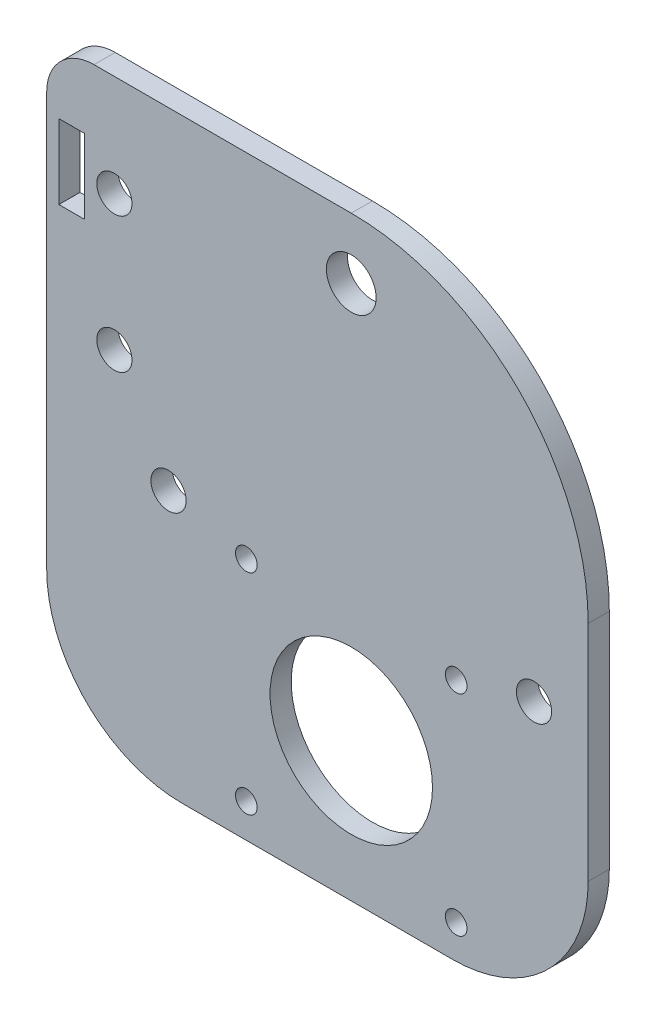
SolidWorks part; units mm, degrees
ref_plane "Front Plane" through (0, 0, 0) normal (0, 0, 1) x (1, 0, 0)
ref_plane "Top Plane" through (0, 0, 0) normal (0, 1, 0) x (1, 0, 0)
ref_plane "Right Plane" through (0, 0, 0) normal (1, 0, 0) x (0, 0, -1)
sketch "Model" plane through (0, 0, 0) normal (0, 0, 1) x (1, 0, 0)
  line L0 (80, 20) -> (80, 53)
  line L1 (20, 0) -> (60, 0)
  line L2 (0, 81) -> (0, 20)
  line L3 (45, 88) -> (7, 88)
  line L4 (1.8, 78.5) -> (1.8, 67.5)
  line L5 (1.8, 67.5) -> (5.5607, 67.5)
  line L6 (5.5607, 67.5) -> (5.5607, 78.5)
  line L7 (5.5607, 78.5) -> (1.8, 78.5)
  circle A0 centre (10, 73) radius 2.6
  circle A1 centre (45, 20.5) radius 12
  circle A2 centre (18, 39) radius 2.6
  circle A3 centre (60.5, 36) radius 1.6
  circle A4 centre (29.5, 5) radius 1.6
  circle A5 centre (45, 79) radius 3.675
  circle A6 centre (10, 53) radius 2.6
  circle A7 centre (29.5, 36) radius 1.6
  circle A8 centre (60.5, 5) radius 1.6
  circle A9 centre (72, 39) radius 2.6
  arc A10 (80, 53) -> (45, 88) centre (45, 53) ccw
  arc A11 (60, 0) -> (80, 20) centre (60, 20) ccw
  arc A12 (0, 20) -> (20, 0) centre (20, 20) ccw
  arc A13 (7, 88) -> (0, 81) centre (7, 81) ccw
  dimension "D1" = 24
  dimension "D4" = 3.2
  dimension "D7" = 31
  dimension "D8" = 31
  dimension "D9" = 5
  dimension "D11" = 20
  dimension "D12" = 20
  dimension "D13" = 35
  dimension "D14" = 7
  dimension "D15" = 5.2
  dimension "D21" = 3
  dimension "D23" = 54
  dimension "D25" = 53
  dimension "D26" = 10
  dimension "D27" = 7.35
  dimension "D29" = 11.5
  dimension "D30" = 20.5
  dimension "D31" = 60
  dimension "D32" = 45
  dimension "D2" = 88
  dimension "D3" = 80
  dimension "D5" = 15.5
  dimension "D6" = 15.5
  dimension "D10" = 29.5
  dimension "D16" = 20
  dimension "D17" = 3.7607
  dimension "D18" = 11
  dimension "D19" = 67.5
  dimension "D20" = 40
  dimension "D22" = 40
  dimension "D24" = 1.8
  dimension "D28" = 27
extrude "Boss-Extrude1" add sketch "Model" along normal blind 3.125
